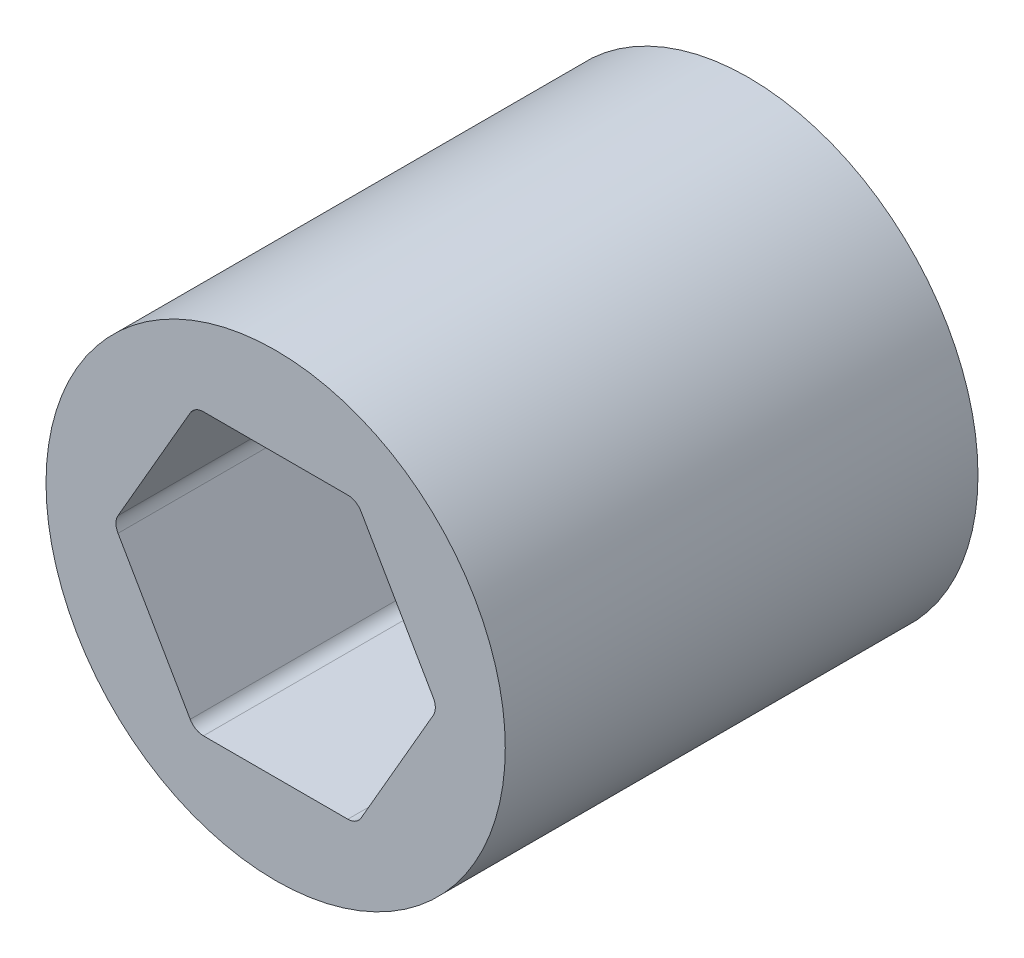
SolidWorks part; units mm, degrees
ref_plane "Alzado" through (0, 0, 0) normal (0, 0, 1) x (1, 0, 0)
ref_plane "Planta" through (0, 0, 0) normal (0, 1, 0) x (1, 0, 0)
ref_plane "Vista lateral" through (0, 0, 0) normal (1, 0, 0) x (0, 0, -1)
sketch "Croquis1" plane through (0, 0, 0) normal (0, 0, 1) x (1, 0, 0)
  line L1 (3.5929, 6.985) -> (-3.5929, 6.985)
  line L2 (-4.2528, 6.604) -> (-7.8456, 0.381)
  line L3 (-7.8456, -0.381) -> (-4.2528, -6.604)
  line L4 (-3.5929, -6.985) -> (3.5929, -6.985)
  line L5 (4.2528, -6.604) -> (7.8456, -0.381)
  line L6 (7.8456, 0.381) -> (4.2528, 6.604)
  circle A0 centre (0, 0) radius 6.985 construction
  circle A1 centre (0, 0) radius 11.43
  arc A2 (-7.8456, 0.381) -> (-7.8456, -0.381) centre (-7.1857, 0) ccw
  arc A3 (-4.2528, -6.604) -> (-3.5929, -6.985) centre (-3.5929, -6.223) ccw
  arc A4 (3.5929, -6.985) -> (4.2528, -6.604) centre (3.5929, -6.223) ccw
  arc A5 (7.8456, -0.381) -> (7.8456, 0.381) centre (7.1857, 0) ccw
  arc A6 (3.5929, 6.985) -> (4.2528, 6.604) centre (3.5929, 6.223) cw
  arc A7 (-3.5929, 6.985) -> (-4.2528, 6.604) centre (-3.5929, 6.223) ccw
  dimension "D1" = 13.97
  dimension "D2" = 22.86
  dimension "D3" = 0.762
extrude "Saliente-Extruir1" add sketch "Croquis1" along normal mid plane 23.5282
